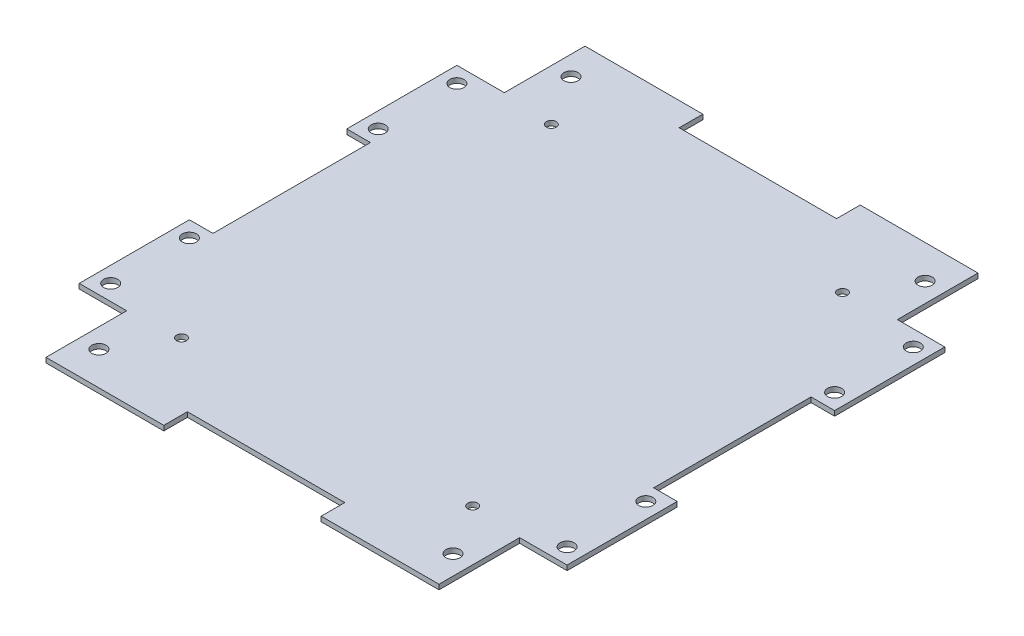
SolidWorks part; units mm, degrees
ref_plane "Front Plane" through (0, 0, 0) normal (0, 0, 1) x (1, 0, 0)
ref_plane "Top Plane" through (0, 0, 0) normal (0, 1, 0) x (1, 0, 0)
ref_plane "Right Plane" through (0, 0, 0) normal (1, 0, 0) x (0, 0, -1)
sketch "Sketch1" plane through (0, 0, 0) normal (0, 1, 0) x (1, 0, 0)
  line L0 (-25.4, 86.995) -> (-63.4314, 86.995)
  line L1 (-88.9, -101.6) -> (88.9, -101.6) construction
  line L2 (101.6, -88.9) -> (101.6, 88.9) construction
  line L3 (88.9, 101.6) -> (-88.9, 101.6) construction
  line L4 (-78.74, -60.96) -> (-63.4314, -60.96)
  line L5 (-63.4314, -60.96) -> (-63.4314, -86.995)
  line L6 (-63.4314, -86.995) -> (-25.4, -86.995)
  line L7 (63.4314, -86.995) -> (63.4314, -60.96)
  line L8 (63.4314, -60.96) -> (78.74, -60.96)
  line L9 (78.74, -60.96) -> (78.74, -25.4)
  line L10 (78.74, 60.96) -> (63.4314, 60.96)
  line L11 (63.4314, 60.96) -> (63.4314, 86.995)
  line L12 (63.4314, 86.995) -> (25.4, 86.995)
  line L13 (-63.4314, 86.995) -> (-63.4314, 60.96)
  line L14 (-63.4314, 60.96) -> (-78.74, 60.96)
  line L15 (-78.74, 60.96) -> (-78.74, 25.4)
  line L16 (-78.74, -25.4) -> (-78.74, -60.96)
  line L17 (-78.74, -25.4) -> (-71.12, -25.4)
  line L19 (-78.74, 25.4) -> (-71.12, 25.4)
  line L20 (-71.12, -25.4) -> (-71.12, 25.4)
  line L22 (-25.4, 86.995) -> (-25.4, 79.375)
  line L23 (-25.4, 79.375) -> (25.4, 79.375)
  line L24 (25.4, 86.995) -> (25.4, 79.375)
  line L25 (78.74, 25.4) -> (71.12, 25.4)
  line L27 (78.74, -25.4) -> (71.12, -25.4)
  line L28 (71.12, 25.4) -> (71.12, -25.4)
  line L30 (25.4, -86.995) -> (25.4, -79.375)
  line L31 (25.4, -79.375) -> (-25.4, -79.375)
  line L32 (-25.4, -86.995) -> (-25.4, -79.375)
  line L33 (78.74, 25.4) -> (78.74, 60.96)
  line L34 (25.4, -86.995) -> (63.4314, -86.995)
  line L35 (-101.6, 88.9) -> (-101.6, -88.9) construction
  arc A0 (88.9, -101.6) -> (101.6, -88.9) centre (88.9, -88.9) ccw construction
  arc A1 (-101.6, -88.9) -> (-88.9, -101.6) centre (-88.9, -88.9) ccw construction
  arc A2 (101.6, 88.9) -> (88.9, 101.6) centre (88.9, 88.9) ccw construction
  arc A3 (-101.6, 88.9) -> (-88.9, 101.6) centre (-88.9, 88.9) cw construction
  circle A4 centre (-57.15, 76.2) radius 2.286
  circle A5 centre (57.15, 76.2) radius 2.286
  circle A6 centre (57.15, -76.2) radius 2.286
  circle A7 centre (-57.15, -76.2) radius 2.286
  point P3 (0, 101.6)
  point P5 (101.6, 0)
  point P13 (101.6, 101.6)
  point P16 (-101.6, 101.6)
  point P38 (-71.12, 0)
  point P55 (0, -79.375)
  point P56 (0, 79.375)
  point P57 (71.12, 0)
  dimension "D2" = 12.7
  dimension "D11" = 4.572
  dimension "D8" = 44.45
  dimension "D1" = 203.2
  dimension "D3" = 203.2
  dimension "D4" = 22.86
  dimension "D5" = 15.3086
  dimension "D6" = 35.56
  dimension "D7" = 173.99
  dimension "D12" = 50.8
  dimension "D13" = 25.4
  dimension "D14" = 44.45
  dimension "D15" = 25.4
  dimension "D18" = 7.62
extrude "Main Body" add sketch "Sketch1" along normal blind 1.5875
sketch "Sketch2" plane through (0, 1.5875, 0) normal (0, 1, 0) x (1, 0, 0)
  line L0 (0, -1000) -> (0, 49000) construction
  line L1 (-1000, 0) -> (49000, 0) construction
  line L2 (-78.74, -60.96) -> (-63.4314, -60.96) construction
  line L3 (-71.12, -25.4) -> (-78.74, -25.4) construction
  line L4 (-78.74, -25.4) -> (-78.74, -60.96) construction
  circle A0 centre (-73.66, -30.48) radius 2.286
  circle A1 centre (-73.66, -55.88) radius 2.286
  circle A2 centre (73.66, -55.88) radius 2.286
  circle A3 centre (73.66, -30.48) radius 2.286
  circle A4 centre (73.66, 30.48) radius 2.286
  circle A5 centre (73.66, 55.88) radius 2.286
  circle A6 centre (-73.66, 55.88) radius 2.286
  circle A7 centre (-73.66, 30.48) radius 2.286
  dimension "D1" = 4.572
  dimension "D2" = 5.08
  dimension "D3" = 5.08
  dimension "D4" = 5.08
extrude "Mount Holes" cut sketch "Sketch2" against normal through all
sketch "Sketch3" plane through (0, 1.5875, 0) normal (0, 1, 0) x (1, 0, 0)
  line L1 (-50.8, 63.5) -> (50.8, 63.5) construction
  line L2 (-50.8, 63.5) -> (-50.8, -63.5) construction
  line L3 (-50.8, -63.5) -> (50.8, -63.5) construction
  line L4 (50.8, 63.5) -> (50.8, -63.5) construction
  circle A0 centre (46.99, -59.69) radius 1.5875
  circle A1 centre (-46.99, -59.69) radius 1.5875
  circle A2 centre (-46.99, 59.69) radius 1.5875
  circle A3 centre (46.99, 59.69) radius 1.5875
  point P5 (50.8, 0)
  point P7 (0, 63.5)
  dimension "D3" = 3.81
  dimension "D4" = 3.81
  dimension "D5" = 3.175
  dimension "D8" = 3.81
  dimension "D9" = 3.81
  dimension "D10" = 3.81
  dimension "D1" = 101.6
  dimension "D2" = 127
  dimension "D6" = 2
  dimension "D7" = 2
extrude "Old PCB Holes" cut sketch "Sketch3" against normal blind 2.54
